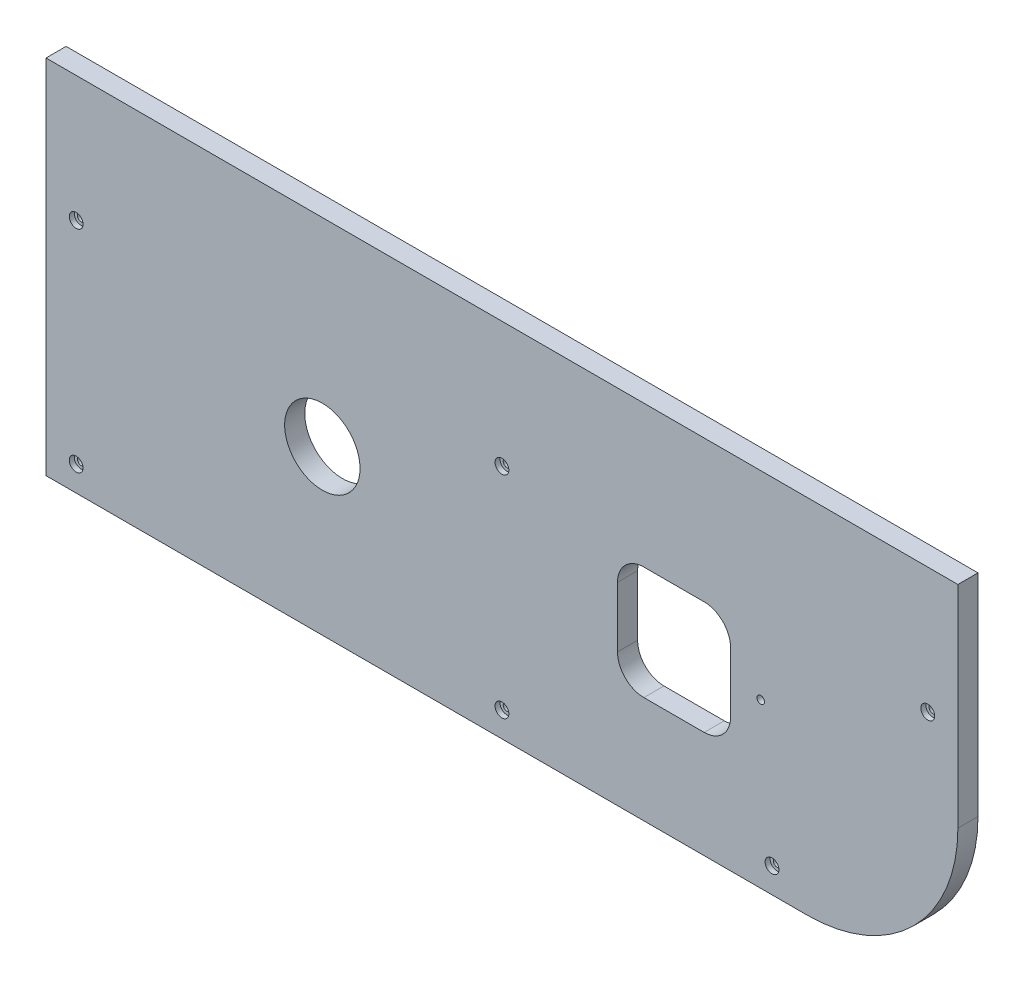
SolidWorks part; units mm, degrees
ref_plane "Plan de face" through (0, 0, 0) normal (0, 0, 1) x (1, 0, 0)
ref_plane "Plan de dessus" through (0, 0, 0) normal (0, 1, 0) x (1, 0, 0)
ref_plane "Plan de droite" through (0, 0, 0) normal (1, 0, 0) x (0, 0, -1)
sketch "Esquisse1" plane through (0, 0, 0) normal (0, 0, 1) x (1, 0, 0)
  line L1 (-162, 973.5) -> (-162, -193) construction
  line L2 (-162, -49) -> (201, -49)
  line L3 (-162, -49) -> (-162, -193)
  line L4 (-162, -193) -> (141, -193)
  line L5 (201, -49) -> (201, -133)
  line L6 (-201, -193) -> (141, -193) construction
  line L7 (201, -133) -> (201, 0) construction
  line L8 (-181, 0) -> (181, 0) construction
  arc A0 (141, -193) -> (201, -133) centre (141, -133) ccw
  dimension "D2" = 60
  dimension "D1" = 49
extrude "Boss.-Extru.1" add sketch "Esquisse1" along normal blind 8
sketch "Esquisse2" plane through (0, 0, 8) normal (0, 0, 1) x (1, 0, 0)
  line L0 (-162, -49) -> (-162, -193) construction
  line L1 (76, -150.5) -> (100, -150.5)
  line L2 (110.5, -140) -> (110.5, -116)
  line L3 (100, -105.5) -> (76, -105.5)
  line L4 (65.5, -116) -> (65.5, -140)
  line L5 (-162, 973.5) -> (-162, -193) construction
  circle A0 centre (-52, -128) radius 15
  arc A1 (65.5, -140) -> (76, -150.5) centre (76, -140) ccw
  arc A2 (100, -150.5) -> (110.5, -140) centre (100, -140) ccw
  arc A3 (110.5, -116) -> (100, -105.5) centre (100, -116) ccw
  arc A4 (76, -105.5) -> (65.5, -116) centre (76, -116) ccw
  circle A5 centre (122.5, -128) radius 1.5
  point P4 (-162, -121)
  point P6 (65.5, -128)
  point P12 (110.5, -128)
  dimension "D1" = 30
  dimension "D4" = 10.5
  dimension "D7" = 3
  dimension "D2" = 7
  dimension "D3" = 110
  dimension "D5" = 24
  dimension "D6" = 227.5
  dimension "D8" = 12
extrude "Enlèv. mat.-Extru.1" cut sketch "Esquisse2" against normal through all
hole_wizard "Chambrage pour vis à tête cylindrique courte six pans creux M31" positions "Esquisse3" profile "Esquisse4" counterbore size "M3" standard "DIN" end condition through all
sketch "Esquisse3" plane through (0, 0, 8) normal (0, 0, 1) x (1, 0, 0)
  line L0 (201, -105) -> (-171, -105) construction
  line L1 (-162, 973.5) -> (-162, -193) construction
  line L2 (-162, -193) -> (141, -193) construction
  line L3 (201, -49) -> (-162, -49) construction
  line L4 (201, -133) -> (201, -49) construction
  point P0 (-150, -99)
  point P2 (19.5, -99)
  point P4 (189, -99)
  point P6 (-150, -183)
  point P8 (19.5, -183)
  point P10 (127, -183)
  point P25 (19.5, -49)
  dimension "D1" = 6
  dimension "D2" = 12
  dimension "D3" = 10
  dimension "D4" = 12
  dimension "D5" = 14
sketch "Esquisse4" plane through (-150, -99, 8) normal (1, 0, 0) x (0, -1, 0)
  line L0 (0, 0) -> (0, 8)
  line L1 (0, 8) -> (1.5, 8)
  line L3 (1.5, 8) -> (1.5, 2)
  line L4 (1.5, 2) -> (2.75, 2)
  line L5 (2.75, 2) -> (2.75, 0)
  line L7 (2.75, 0) -> (0, 0)
  line L11 (0, -6.35) -> (0, 107.95) construction
  dimension "Diamètre du perçage jusqu'au prochain" = 3
  dimension "Profondeur du perçage jusqu'au prochain" = 8
  dimension "Diamètre du chambrage" = 5.5
  dimension "Profondeur du chambrage" = 2
